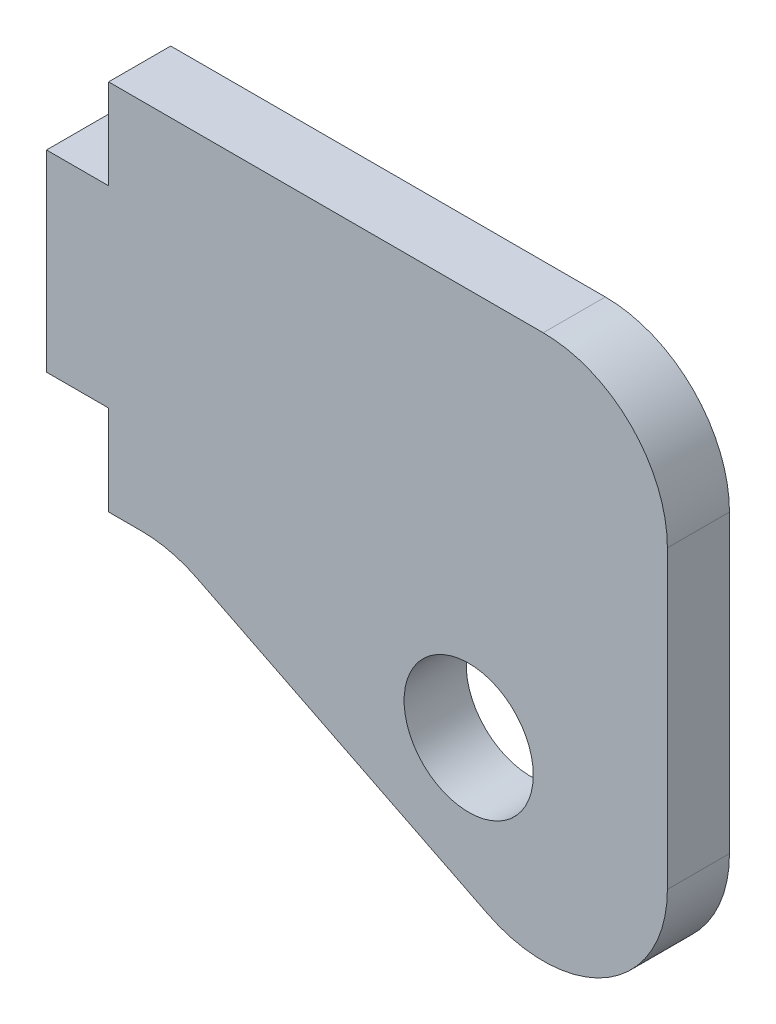
SolidWorks part; units mm, degrees
material "AISI 4340 Steel, normalized"
ref_plane "X-Y Datum" through (0, 0, 0) normal (0, 0, 1) x (1, 0, 0)
ref_plane "X-Z Datum" through (0, 0, 0) normal (0, 1, 0) x (1, 0, 0)
ref_plane "Y-Z Datum" through (0, 0, 0) normal (1, 0, 0) x (0, 0, -1)
sketch "Sketch1" plane through (0, 0, 0) normal (0, 0, 1) x (1, 0, 0)
  line L0 (0, -9.525) -> (6.35, -9.525)
  line L2 (0, 9.525) -> (0, -9.525)
  line L5 (6.35, -9.525) -> (31.75, -22.225)
  line L6 (31.75, -22.225) -> (31.75, 9.525)
  line L7 (31.75, 9.525) -> (0, 9.525)
  point P5 (0, 0)
  dimension "D1" = 19.05
  dimension "D2" = 31.75
  dimension "D3" = 6.35
  dimension "D4" = 31.75
extrude "Boss-Extrude1" add sketch "Sketch1" along normal blind 3.175
fillet "Fillet1" radius 6.35 3 edges at (31.75, 9.525, 1.5875) (31.75, -22.225, 1.5875) (6.35, -9.525, 1.5875)
sketch "Sketch3" plane through (0, 0, 3.175) normal (0, 0, 1) x (1, 0, 0)
  circle A0 centre (21.5883, -10.3159) radius 3.302
  dimension "D1" = 6.604
extrude "Cut-Extrude1" cut sketch "Sketch3" against normal blind 3.175
sketch "Sketch4" plane through (0, 0, 3.175) normal (0, 0, 1) x (1, 0, 0)
  line L0 (0, 9.525) -> (0, -9.525) construction
  line L5 (0, 9.525) -> (3.175, 9.525)
  line L6 (0, 9.525) -> (0, 4.9213)
  line L7 (0, 4.9213) -> (3.175, 4.9213)
  line L8 (3.175, 9.525) -> (3.175, 4.9213)
  line L10 (0, -9.525) -> (3.175, -9.525)
  line L11 (0, -9.525) -> (0, -4.9213)
  line L12 (0, -4.9213) -> (3.175, -4.9213)
  line L13 (3.175, -9.525) -> (3.175, -4.9213)
  dimension "D1" = 3.175
  dimension "D2" = 3.175
  dimension "D3" = 9.8425
extrude "Cut-Extrude2" cut sketch "Sketch4" against normal blind 3.175
